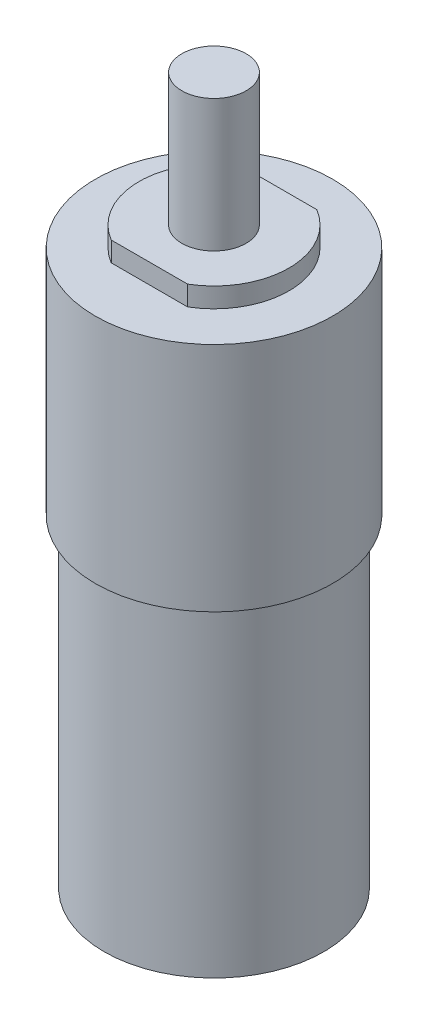
SolidWorks part; units mm, degrees
ref_plane "Front Plane" through (0, 0, 0) normal (0, 0, 1) x (1, 0, 0)
ref_plane "Top Plane" through (0, 0, 0) normal (0, 1, 0) x (1, 0, 0)
ref_plane "Right Plane" through (0, 0, 0) normal (1, 0, 0) x (0, 0, -1)
sketch "Sketch1" plane through (0, 0, 0) normal (0, 1, 0) x (1, 0, 0)
  circle A0 centre (0, 0) radius 10.16
  dimension "D1" = 20.32
extrude "Boss-Extrude1" add sketch "Sketch1" along normal blind 29.8958
sketch "Sketch2" plane through (0, 29.8958, 0) normal (0, 1, 0) x (1, 0, 0)
  circle A0 centre (0, 0) radius 10.9728
  dimension "D1" = 21.9456
extrude "Boss-Extrude2" add sketch "Sketch2" along normal blind 21.4122
sketch "Sketch3" plane through (0, 51.308, 0) normal (0, 1, 0) x (1, 0, 0)
  circle A0 centre (0, 0) radius 6.9342
  dimension "D1" = 13.8684
extrude "Boss-Extrude3" add sketch "Sketch3" along normal blind 1.8288
sketch "Sketch4" plane through (0, 53.1368, 0) normal (0, 1, 0) x (1, 0, 0)
  circle A0 centre (0, 0) radius 2.9718
  dimension "D1" = 5.9436
extrude "Boss-Extrude4" add sketch "Sketch4" along normal blind 65.3542 from surface at -53.1368 starting at face at (0, 0, 10.16)
sketch "Sketch5" plane through (0, 53.1368, 0) normal (0, 1, 0) x (1, 0, 0)
  line L0 (-3.529, 5.969) -> (3.529, 5.969)
  line L2 (3.529, -5.969) -> (-3.529, -5.969)
  arc A0 (-3.529, -5.969) -> (3.529, -5.969) centre (0, 0) ccw
  arc A2 (3.529, 5.969) -> (-3.529, 5.969) centre (0, 0) ccw
  circle A3 centre (0, 0) radius 6.9342 construction
  dimension "D1" = 11.938
extrude "Cut-Extrude1" cut sketch "Sketch5" against normal up to surface (1.8288 mm away) up to face at (0, 51.308, 6.9342)
